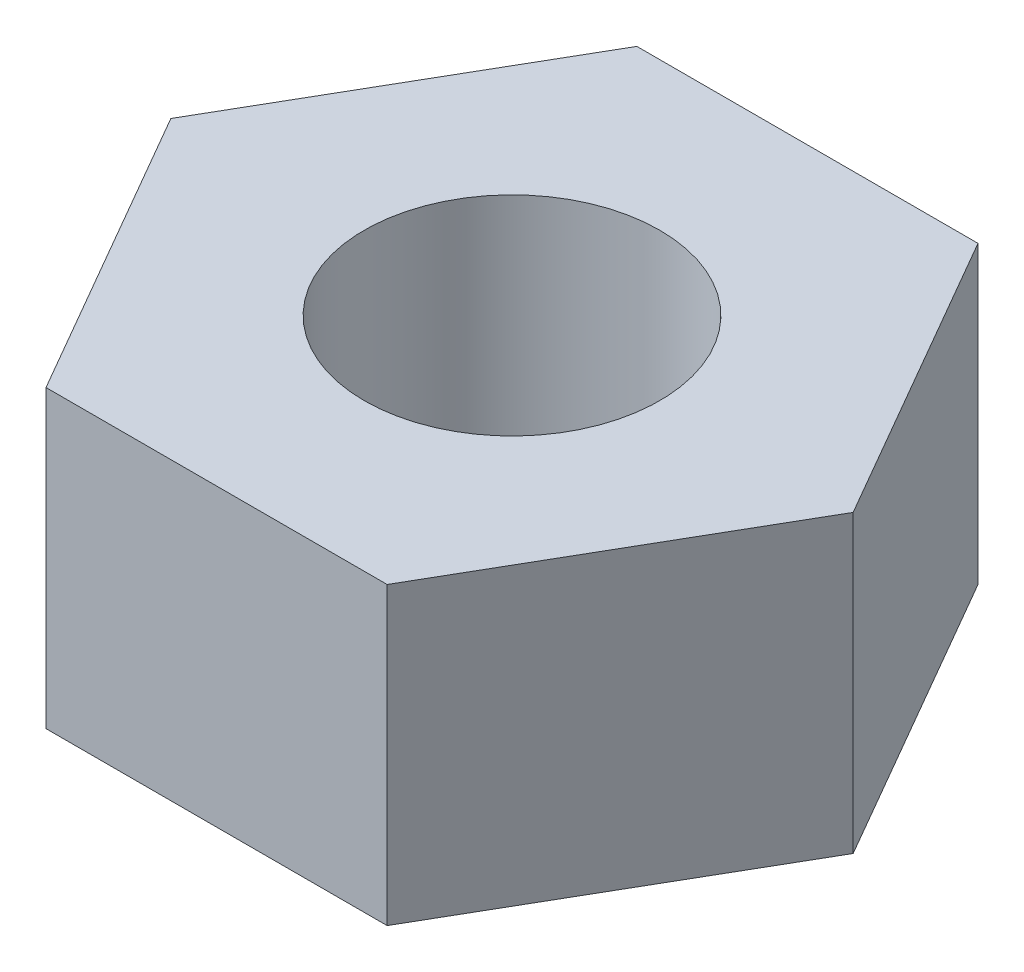
SolidWorks part; units mm, degrees
ref_plane "Front Plane" through (0, 0, 0) normal (0, 0, 1) x (1, 0, 0)
ref_plane "Top Plane" through (0, 0, 0) normal (0, 1, 0) x (1, 0, 0)
ref_plane "Right Plane" through (0, 0, 0) normal (1, 0, 0) x (0, 0, -1)
sketch "Sketch1" plane through (0, 0, 0) normal (0, 1, 0) x (1, 0, 0)
  line L1 (2.3094, 4) -> (-2.3094, 4)
  line L2 (-2.3094, 4) -> (-4.6188, 0)
  line L3 (-4.6188, 0) -> (-2.3094, -4)
  line L4 (-2.3094, -4) -> (2.3094, -4)
  line L5 (2.3094, -4) -> (4.6188, 0)
  line L6 (4.6188, 0) -> (2.3094, 4)
  circle A0 centre (0, 0) radius 2
  circle A1 centre (0, 0) radius 4 construction
  dimension "D1" = 4
  dimension "D2" = 8
extrude "Boss-Extrude1" add sketch "Sketch1" along normal mid plane 4 contours L1 L2 L3 L4 L5 L6
